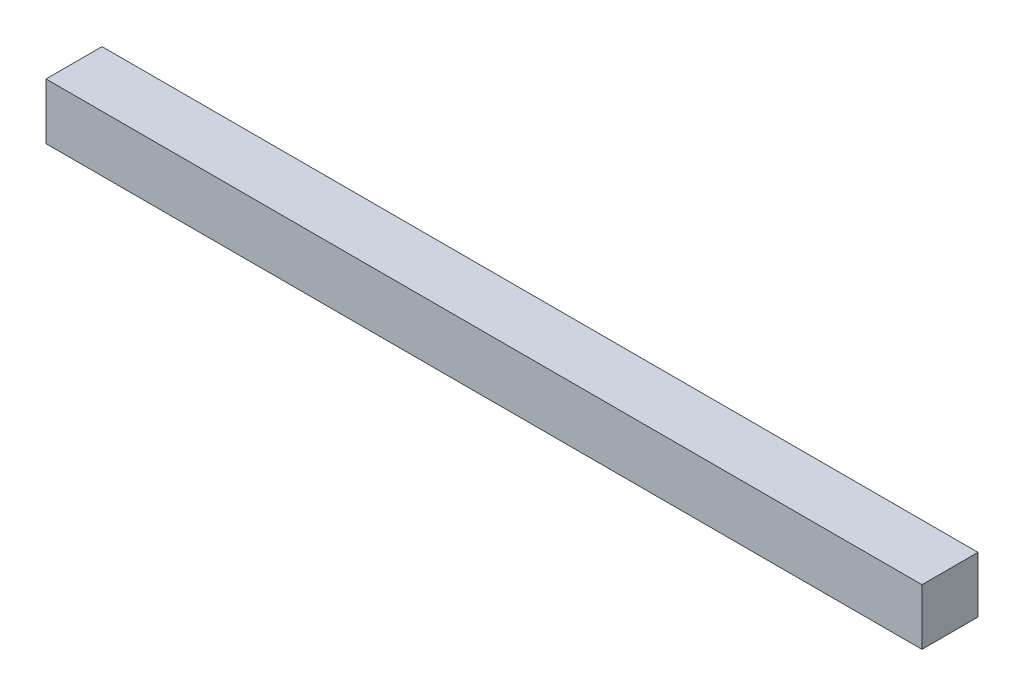
SolidWorks part; units mm, degrees
material "AISI 304"
ref_plane "Front Plane" through (0, 0, 0) normal (0, 0, 1) x (1, 0, 0)
ref_plane "Top Plane" through (0, 0, 0) normal (0, 1, 0) x (1, 0, 0)
ref_plane "Right Plane" through (0, 0, 0) normal (1, 0, 0) x (0, 0, -1)
sketch "Sketch1" plane through (0, 0, 0) normal (0, 1, 0) x (1, 0, 0)
  line L1 (0, 0) -> (46.9, 0)
  line L2 (0, 0) -> (0, 3)
  line L3 (0, 3) -> (46.9, 3)
  line L4 (46.9, 0) -> (46.9, 3)
  dimension "D1" = 46.9
  dimension "D2" = 3
extrude "Boss-Extrude1" add sketch "Sketch1" along normal blind 3
